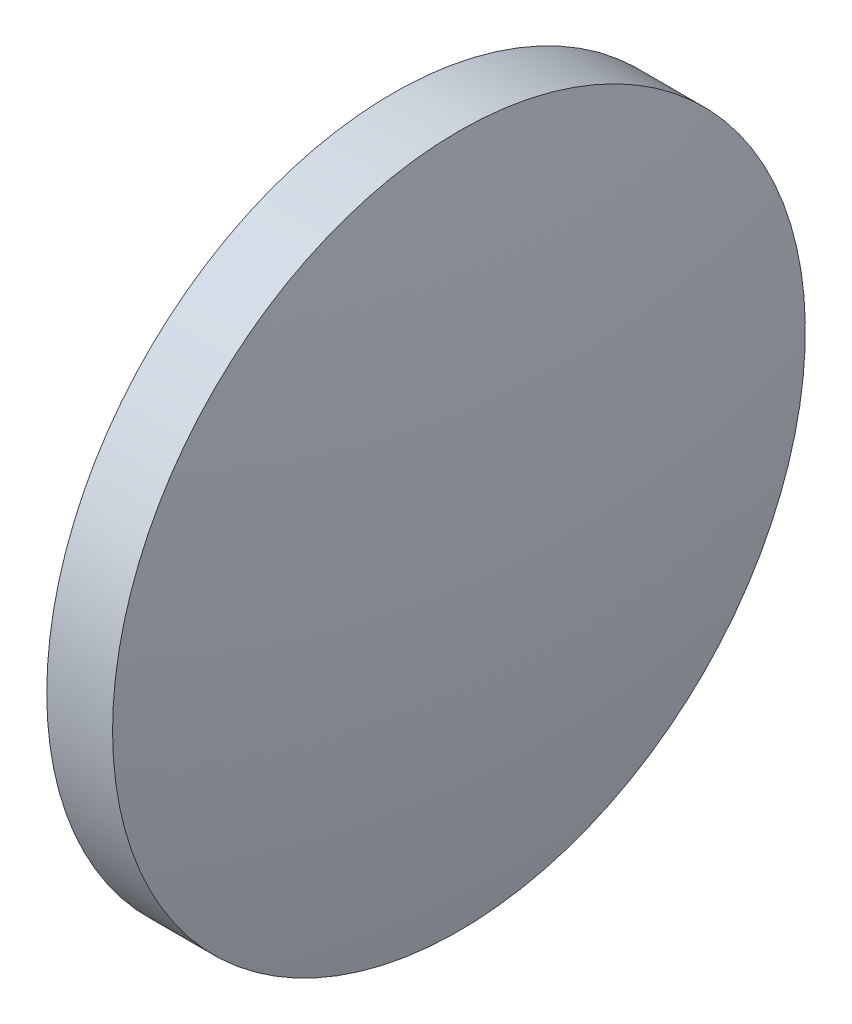
SolidWorks part; units mm, degrees
ref_plane "前视基准面" through (0, 0, 0) normal (0, 0, 1) x (1, 0, 0)
ref_plane "上视基准面" through (0, 0, 0) normal (0, 1, 0) x (1, 0, 0)
ref_plane "右视基准面" through (0, 0, 0) normal (1, 0, 0) x (0, 0, -1)
sketch "草图1" plane through (0, 0, 0) normal (0, 0, 1) x (1, 0, 0)
  line L0 (610.4244, 147.6021) -> (608.1244, 147.6021)
  line L14 (606.2016, 147.6021) -> (614.4689, 147.6021) construction
  line L15 (608.1244, 147.6021) -> (608.1244, 155.6021)
  line L19 (608.1244, 155.6021) -> (609.6444, 155.6021)
  arc A2 (610.4244, 147.6021) -> (609.6444, 155.6021) centre (569.0087, 147.6021) ccw
revolve "旋转3" add sketch "草图1" angle 360 about L14
